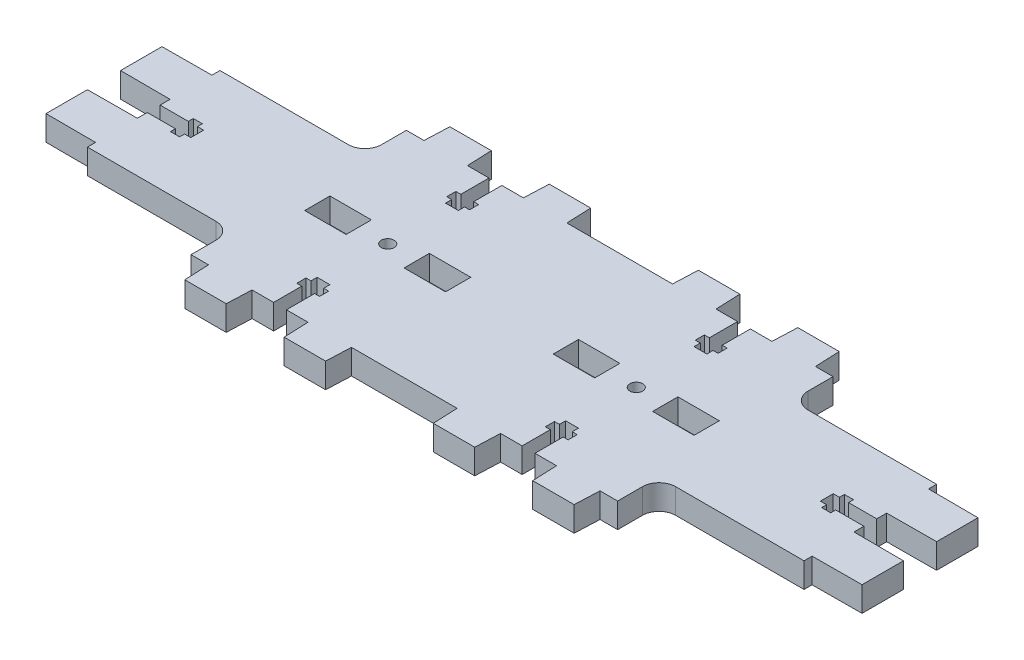
SolidWorks part; units mm, degrees
ref_plane "Спереди" through (0, 0, 0) normal (0, 0, 1) x (1, 0, 0)
ref_plane "Сверху" through (0, 0, 0) normal (0, 1, 0) x (1, 0, 0)
ref_plane "Справа" through (0, 0, 0) normal (1, 0, 0) x (0, 0, -1)
sketch "Эскиз1" plane through (0, 0, 0) normal (0, 1, 0) x (1, 0, 0)
  line L0 (4.2616, -5.7762) -> (4.2616, 0.3238)
  line L1 (14.2616, -5.7762) -> (4.2616, -5.7762)
  line L2 (14.2616, 0.3238) -> (14.2616, -5.7762)
  line L3 (4.2616, 0.3238) -> (14.2616, 0.3238)
  line L4 (-19.7384, -5.7762) -> (-19.7384, 0.3238)
  line L5 (-9.7384, -5.7762) -> (-19.7384, -5.7762)
  line L6 (-9.7384, 0.3238) -> (-9.7384, -5.7762)
  line L7 (-19.7384, 0.3238) -> (-9.7384, 0.3238)
  line L8 (40.2616, 0.3238) -> (40.2616, -5.7762)
  line L9 (40.2616, -5.7762) -> (50.2616, -5.7762)
  line L10 (50.2616, -5.7762) -> (50.2616, 0.3238)
  line L11 (50.2616, 0.3238) -> (40.2616, 0.3238)
  line L12 (40.2616, 29.2738) -> (40.0116, 23.2738)
  line L13 (50.2616, 29.2738) -> (40.2616, 29.2738)
  line L14 (50.5116, 23.2738) -> (50.2616, 29.2738)
  line L15 (55.7116, 23.2738) -> (50.5116, 23.2738)
  line L16 (55.7116, 16.4738) -> (55.7116, 23.2738)
  line L17 (54.5116, 16.4738) -> (55.7116, 16.4738)
  line L18 (54.5116, 14.2738) -> (54.5116, 16.4738)
  line L19 (55.7116, 14.2738) -> (54.5116, 14.2738)
  line L20 (55.7116, 12.7738) -> (55.7116, 14.2738)
  line L21 (58.8116, 12.7738) -> (55.7116, 12.7738)
  line L22 (58.8116, 14.2738) -> (58.8116, 12.7738)
  line L23 (60.0116, 14.2738) -> (58.8116, 14.2738)
  line L24 (60.0116, 16.4738) -> (60.0116, 14.2738)
  line L25 (58.8116, 16.4738) -> (60.0116, 16.4738)
  line L26 (58.8116, 23.2738) -> (58.8116, 16.4738)
  line L27 (64.0116, 23.2738) -> (58.8116, 23.2738)
  line L28 (64.2616, 29.2738) -> (64.0116, 23.2738)
  line L29 (74.2616, 29.2738) -> (64.2616, 29.2738)
  line L30 (74.5116, 23.2738) -> (74.2616, 29.2738)
  line L31 (78.7616, 23.2738) -> (74.5116, 23.2738)
  line L32 (78.7616, 17.2738) -> (78.7616, 23.2738)
  line L33 (113.7616, 13.2738) -> (82.7616, 13.2738)
  line L34 (113.7616, 11.3238) -> (113.7616, 13.2738)
  line L35 (125.7616, 11.2738) -> (113.7616, 11.3238)
  line L36 (125.7616, 1.2738) -> (125.7616, 11.2738)
  line L37 (113.7616, 1.2238) -> (125.7616, 1.2738)
  line L38 (113.7616, -1.1762) -> (113.7616, 1.2238)
  line L39 (106.9616, -1.1762) -> (113.7616, -1.1762)
  line L40 (106.9616, 0.0238) -> (106.9616, -1.1762)
  line L41 (104.7616, 0.0238) -> (106.9616, 0.0238)
  line L42 (104.7616, -1.1762) -> (104.7616, 0.0238)
  line L43 (103.2616, -1.1762) -> (104.7616, -1.1762)
  line L44 (103.2616, -4.2762) -> (103.2616, -1.1762)
  line L45 (104.7616, -4.2762) -> (103.2616, -4.2762)
  line L46 (104.7616, -5.4762) -> (104.7616, -4.2762)
  line L47 (106.9616, -5.4762) -> (104.7616, -5.4762)
  line L48 (106.9616, -4.2762) -> (106.9616, -5.4762)
  line L49 (113.7616, -4.2762) -> (106.9616, -4.2762)
  line L50 (113.7616, -6.6762) -> (113.7616, -4.2762)
  line L51 (125.7616, -6.7262) -> (113.7616, -6.6762)
  line L52 (125.7616, -16.7262) -> (125.7616, -6.7262)
  line L53 (113.7616, -16.7762) -> (125.7616, -16.7262)
  line L54 (113.7616, -18.7262) -> (113.7616, -16.7762)
  line L55 (82.7616, -18.7262) -> (113.7616, -18.7262)
  line L56 (78.7616, -28.7262) -> (78.7616, -22.7262)
  line L57 (74.5116, -28.7262) -> (78.7616, -28.7262)
  line L58 (74.2616, -34.7262) -> (74.5116, -28.7262)
  line L59 (64.2616, -34.7262) -> (74.2616, -34.7262)
  line L60 (64.0116, -28.7262) -> (64.2616, -34.7262)
  line L61 (58.8116, -28.7262) -> (64.0116, -28.7262)
  line L62 (58.8116, -21.9262) -> (58.8116, -28.7262)
  line L63 (60.0116, -21.9262) -> (58.8116, -21.9262)
  line L64 (60.0116, -19.7262) -> (60.0116, -21.9262)
  line L65 (58.8116, -19.7262) -> (60.0116, -19.7262)
  line L66 (58.8116, -18.2262) -> (58.8116, -19.7262)
  line L67 (55.7116, -18.2262) -> (58.8116, -18.2262)
  line L68 (55.7116, -19.7262) -> (55.7116, -18.2262)
  line L69 (54.5116, -19.7262) -> (55.7116, -19.7262)
  line L70 (54.5116, -21.9262) -> (54.5116, -19.7262)
  line L71 (55.7116, -21.9262) -> (54.5116, -21.9262)
  line L72 (55.7116, -28.7262) -> (55.7116, -21.9262)
  line L73 (50.5116, -28.7262) -> (55.7116, -28.7262)
  line L74 (50.2616, -34.7262) -> (50.5116, -28.7262)
  line L75 (40.2616, -34.7262) -> (50.2616, -34.7262)
  line L76 (40.0116, -28.7262) -> (40.2616, -34.7262)
  line L77 (14.5116, -28.7262) -> (40.0116, -28.7262)
  line L78 (14.5116, -28.7262) -> (14.2616, -34.7262)
  line L79 (14.2616, -34.7262) -> (4.2616, -34.7262)
  line L80 (4.2616, -34.7262) -> (4.0116, -28.7262)
  line L81 (4.0116, -28.7262) -> (-1.1884, -28.7262)
  line L82 (-1.1884, -28.7262) -> (-1.1884, -21.9262)
  line L83 (-1.1884, -21.9262) -> (0.0116, -21.9262)
  line L84 (0.0116, -21.9262) -> (0.0116, -19.7262)
  line L85 (0.0116, -19.7262) -> (-1.1884, -19.7262)
  line L86 (-1.1884, -19.7262) -> (-1.1884, -18.2262)
  line L87 (-1.1884, -18.2262) -> (-4.2884, -18.2262)
  line L88 (-4.2884, -18.2262) -> (-4.2884, -19.7262)
  line L89 (-4.2884, -19.7262) -> (-5.4884, -19.7262)
  line L90 (-5.4884, -19.7262) -> (-5.4884, -21.9262)
  line L91 (-5.4884, -21.9262) -> (-4.2884, -21.9262)
  line L92 (-4.2884, -21.9262) -> (-4.2884, -28.7262)
  line L93 (-4.2884, -28.7262) -> (-9.4884, -28.7262)
  line L94 (-9.4884, -28.7262) -> (-9.7384, -34.7262)
  line L95 (-19.7384, -34.7262) -> (-19.9884, -28.7262)
  line L96 (-19.9884, -28.7262) -> (-24.2384, -28.7262)
  line L97 (-24.2384, -28.7262) -> (-24.2384, -22.7262)
  line L98 (-28.2384, -18.7262) -> (-59.2384, -18.7262)
  line L99 (-59.2384, -18.7262) -> (-59.2384, -16.7762)
  line L100 (-59.2384, -16.7762) -> (-71.2384, -16.7262)
  line L101 (-71.2384, -16.7262) -> (-71.2384, -6.7262)
  line L102 (-71.2384, -6.7262) -> (-59.2384, -6.6762)
  line L103 (-59.2384, -6.6762) -> (-59.2384, -4.2762)
  line L104 (-59.2384, -4.2762) -> (-52.4384, -4.2762)
  line L105 (-52.4384, -4.2762) -> (-52.4384, -5.4762)
  line L106 (-52.4384, -5.4762) -> (-50.2384, -5.4762)
  line L107 (-50.2384, -5.4762) -> (-50.2384, -4.2762)
  line L108 (-50.2384, -4.2762) -> (-48.7384, -4.2762)
  line L109 (-48.7384, -4.2762) -> (-48.7384, -1.1762)
  line L110 (-48.7384, -1.1762) -> (-50.2384, -1.1762)
  line L111 (-50.2384, -1.1762) -> (-50.2384, 0.0238)
  line L112 (-50.2384, 0.0238) -> (-52.4384, 0.0238)
  line L113 (-52.4384, 0.0238) -> (-52.4384, -1.1762)
  line L114 (-52.4384, -1.1762) -> (-59.2384, -1.1762)
  line L115 (-59.2384, -1.1762) -> (-59.2384, 1.2238)
  line L116 (-59.2384, 1.2238) -> (-71.2384, 1.2738)
  line L117 (-71.2384, 1.2738) -> (-71.2384, 11.2738)
  line L118 (-71.2384, 11.2738) -> (-59.2384, 11.3238)
  line L119 (-59.2384, 11.3238) -> (-59.2384, 13.2738)
  line L120 (-59.2384, 13.2738) -> (-28.2384, 13.2738)
  line L121 (-24.2384, 17.2738) -> (-24.2384, 23.2738)
  line L122 (-24.2384, 23.2738) -> (-19.9884, 23.2738)
  line L123 (-19.9884, 23.2738) -> (-19.7384, 29.2738)
  line L124 (-19.7384, 29.2738) -> (-9.7384, 29.2738)
  line L125 (-9.7384, 29.2738) -> (-9.4884, 23.2738)
  line L126 (-9.4884, 23.2738) -> (-4.2884, 23.2738)
  line L127 (-4.2884, 23.2738) -> (-4.2884, 16.4738)
  line L128 (-4.2884, 16.4738) -> (-5.4884, 16.4738)
  line L129 (-5.4884, 16.4738) -> (-5.4884, 14.2738)
  line L130 (-5.4884, 14.2738) -> (-4.2884, 14.2738)
  line L131 (-4.2884, 14.2738) -> (-4.2884, 12.7738)
  line L132 (-4.2884, 12.7738) -> (-1.1884, 12.7738)
  line L133 (-1.1884, 12.7738) -> (-1.1884, 14.2738)
  line L134 (-1.1884, 14.2738) -> (0.0116, 14.2738)
  line L135 (0.0116, 14.2738) -> (0.0116, 16.4738)
  line L136 (0.0116, 16.4738) -> (-1.1884, 16.4738)
  line L137 (-1.1884, 16.4738) -> (-1.1884, 23.2738)
  line L138 (-1.1884, 23.2738) -> (4.0116, 23.2738)
  line L139 (4.0116, 23.2738) -> (4.2616, 29.2738)
  line L140 (4.2616, 29.2738) -> (14.2616, 29.2738)
  line L141 (14.2616, 29.2738) -> (14.5116, 23.2738)
  line L142 (40.0116, 23.2738) -> (14.5116, 23.2738)
  line L143 (64.2616, 0.3238) -> (64.2616, -5.7762)
  line L144 (64.2616, -5.7762) -> (74.2616, -5.7762)
  line L145 (74.2616, -5.7762) -> (74.2616, 0.3238)
  line L146 (74.2616, 0.3238) -> (64.2616, 0.3238)
  line L147 (-19.7384, -34.7262) -> (-9.7384, -34.7262)
  circle A0 centre (-2.7384, -2.7262) radius 1.55
  circle A1 centre (57.2616, -2.7262) radius 1.55
  arc A2 (78.7616, 17.2738) -> (82.7616, 13.2738) centre (82.7616, 17.2738) ccw
  arc A3 (82.7616, -18.7262) -> (78.7616, -22.7262) centre (82.7616, -22.7262) ccw
  arc A4 (-24.2384, -22.7262) -> (-28.2384, -18.7262) centre (-28.2384, -22.7262) ccw
  arc A5 (-28.2384, 13.2738) -> (-24.2384, 17.2738) centre (-28.2384, 17.2738) ccw
extrude "Бобышка-Вытянуть1" add sketch "Эскиз1" along normal blind 6
